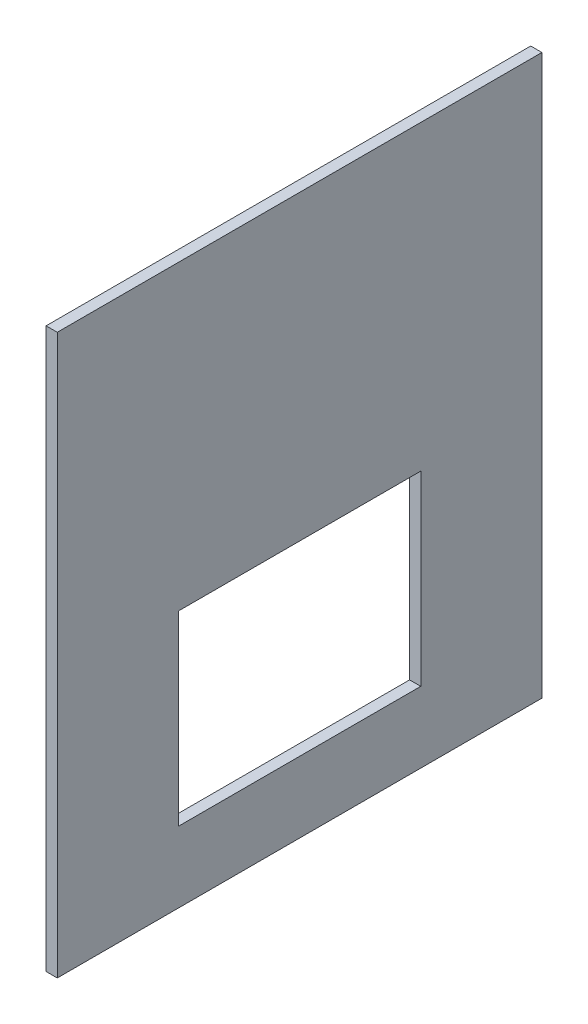
SolidWorks part; units mm, degrees
ref_plane "Front Plane" through (0, 0, 0) normal (0, 0, 1) x (1, 0, 0)
ref_plane "Top Plane" through (0, 0, 0) normal (0, 1, 0) x (1, 0, 0)
ref_plane "Right Plane" through (0, 0, 0) normal (1, 0, 0) x (0, 0, -1)
sketch "Sketch1" plane through (0, 0, 0) normal (1, 0, 0) x (0, 0, -1)
  line L1 (0, 0) -> (130, 0)
  line L2 (0, 0) -> (0, 150)
  line L3 (0, 150) -> (130, 150)
  line L4 (130, 0) -> (130, 150)
  line L5 (32.5, 19) -> (97.5, 19)
  line L6 (32.5, 19) -> (32.5, 69)
  line L7 (32.5, 69) -> (97.5, 69)
  line L8 (97.5, 19) -> (97.5, 69)
  dimension "D1" = 150
  dimension "D2" = 130
  dimension "D3" = 65
  dimension "D4" = 50
  dimension "D5" = 19
  dimension "D6" = 32.5
extrude "Boss-Extrude1" add sketch "Sketch1" along normal blind 3
